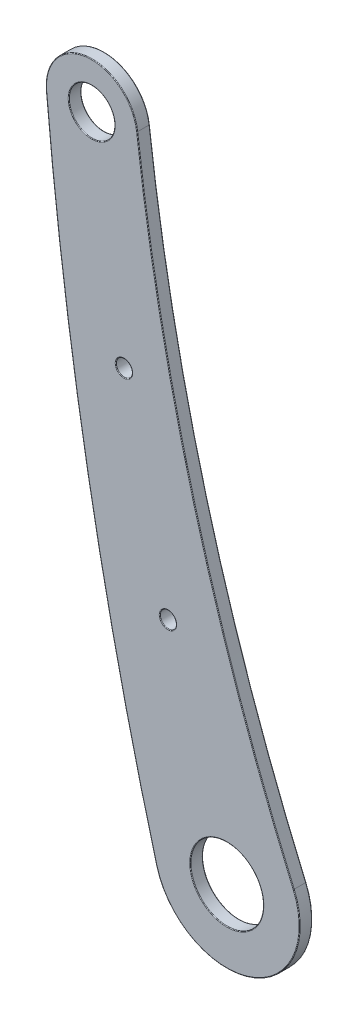
SolidWorks part; units mm, degrees
ref_plane "Płaszczyzna przednia" through (0, 0, 0) normal (0, 0, 1) x (1, 0, 0)
ref_plane "Płaszczyzna górna" through (0, 0, 0) normal (0, 1, 0) x (1, 0, 0)
ref_plane "Płaszczyzna prawa" through (0, 0, 0) normal (1, 0, 0) x (0, 0, -1)
sketch "Szkic1" plane through (0, 0, 0) normal (0, 0, 1) x (1, 0, 0)
  line L0 (-20.22, 57.58) -> (-52.6671, 201.9794) construction
  line L1 (-20.22, 57.58) -> (-52.6671, 201.9794) construction
  circle A0 centre (-52.6671, 201.9794) radius 11 construction
  circle A1 centre (-52.6671, 201.9794) radius 11 construction
  circle A2 centre (-20.22, 57.58) radius 17.5 construction
  circle A3 centre (-20.22, 57.58) radius 17.5 construction
sketch "Szkic2" plane through (0, 0, 0) normal (0, 0, 1) x (1, 0, 0)
  circle A0 centre (-52.6671, 201.9794) radius 5.5
  circle A1 centre (-20.22, 57.58) radius 8.75
  arc A2 (-41.7465, 203.2989) -> (-4.1618, 64.5359) centre (454.6431, 263.2771) ccw
  circle A3 centre (-52.6671, 201.9794) radius 11 construction
  circle A4 centre (-20.22, 57.58) radius 17.5 construction
  arc A5 (-63.6238, 201.005) -> (-37.1052, 52.9823) centre (783.0348, 276.299) ccw
  arc A6 (-52.6671, 201.9794) -> (-20.22, 57.58) centre (691.7396, 293.4051) ccw construction
  arc A7 (-63.6238, 201.005) -> (-41.7465, 203.2989) centre (-52.6671, 201.9794) cw
  arc A8 (-37.1052, 52.9823) -> (-4.1618, 64.5359) centre (-20.22, 57.58) ccw
  point P17 (-44.9212, 152.583)
  point P18 (-34.3508, 105.5417)
  dimension "D1" = 11
  dimension "D2" = 17.5
  dimension "D3" = 850
  dimension "D4" = 500
  dimension "D5" = 750
  dimension "D6" = 50
  dimension "D7" = 50
extrude "Dodanie-wyciągnięcie1" add sketch "Szkic2" along normal blind 3
hole_wizard "Otwór pod śrubę M3.51" positions "Szkic3" profile "Szkic4" hole size "M3.5" standard "ISO" end condition through all
sketch "Szkic3" plane through (0, 0, 3) normal (0, 0, 1) x (1, 0, 0)
  point P0 (-44.9212, 152.583)
  point P3 (-34.3508, 105.5417)
sketch "Szkic4" plane through (-44.9212, 152.583, 3) normal (1, 0, 0) x (0, -1, 0)
  line L0 (0, 0) -> (0, 3)
  line L1 (0, 3) -> (1.95, 3)
  line L2 (1.95, 3) -> (1.95, 0)
  line L5 (1.95, 0) -> (0, 0)
  line L11 (0, -6.35) -> (0, 107.95) construction
  dimension "Średnica otworu na wylot" = 3.9
  dimension "Głębokość otworu na wylot" = 3
fillet "Zaokrąglenie1" radius 0.15 16 edges at (-32.4008, 105.5417, 0) (-47.1671, 201.9794, 0) (-53.6444, 126.4061, 0) (-14.4284, 41.0661, 0) (-27.9674, 132.5596, 0) (-53.8142, 212.9194, 0) (-11.47, 57.58, 0) (-42.9712, 152.583, 0) (-32.4008, 105.5417, 3) (-11.47, 57.58, 3) (-47.1671, 201.9794, 3) (-27.9674, 132.5596, 3) (-14.4284, 41.0661, 3) (-53.6444, 126.4061, 3) (-53.8142, 212.9194, 3) (-42.9712, 152.583, 3)
